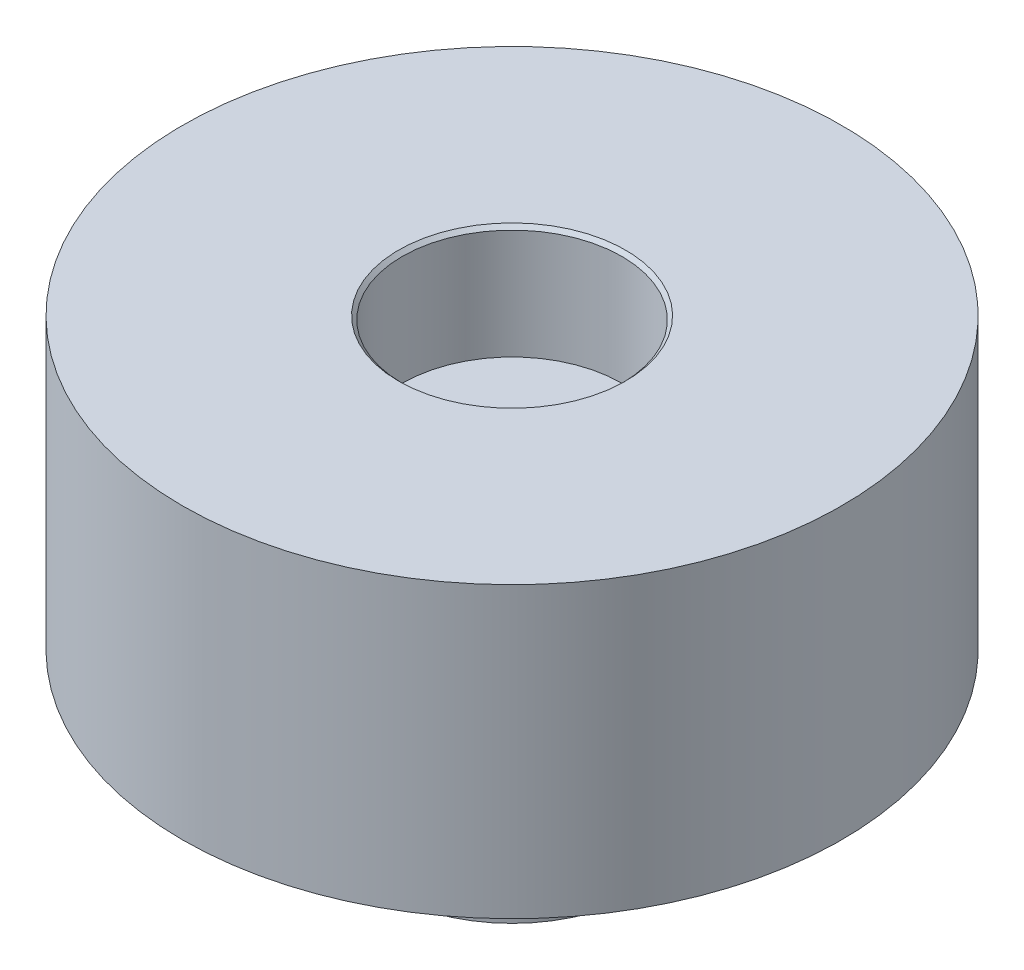
SolidWorks part; units mm, degrees
ref_plane "Front Plane" through (0, 0, 0) normal (0, 0, 1) x (1, 0, 0)
ref_plane "Top Plane" through (0, 0, 0) normal (0, 1, 0) x (1, 0, 0)
ref_plane "Right Plane" through (0, 0, 0) normal (1, 0, 0) x (0, 0, -1)
sketch "Sketch1" plane through (0, 0, 0) normal (0, 1, 0) x (1, 0, 0)
  circle A0 centre (0, 0) radius 9
  dimension "D1" = 18
extrude "Boss-Extrude1" add sketch "Sketch1" along normal blind 7.9
sketch "Sketch2" plane through (0, 7.9, 0) normal (0, 1, 0) x (1, 0, 0)
  circle A0 centre (0, 0) radius 3
  dimension "D1" = 6
extrude "Cut-Extrude1" cut sketch "Sketch2" against normal blind 3.1
sketch "Sketch3" plane through (0, 0, 0) normal (0, -1, 0) x (1, 0, 0)
  circle A0 centre (0, 0) radius 3.5
  dimension "D1" = 7
extrude "Boss-Extrude2" add sketch "Sketch3" along normal blind 4
hole_wizard "Tapped Hole for M2.5x0.45 Helicoil1" positions "Sketch4" profile "Sketch5" tap size "M2.5x0.45" standard "Helicoil® Metric"
sketch "Sketch4" plane through (0, -4, 0) normal (0, -1, 0) x (-1, 0, 0)
  point P0 (0, 0)
sketch "Sketch5" plane through (0, -4, 0) normal (1, 0, 0) x (0, 0, -1)
  line L0 (0, 0) -> (0, 7.6161)
  line L1 (0, 7.6161) -> (1.275, 6.85)
  line L2 (1.275, 6.85) -> (1.275, 0.3225)
  line L3 (1.275, 0.3225) -> (1.5975, 0)
  line L5 (1.5975, 0) -> (0, 0)
  line L6 (-1.275, 0.3225) -> (-1.5975, 0) construction
  line L10 (0, 7.6161) -> (-1.275, 6.85) construction
  line L11 (0, -6.35) -> (0, 107.95) construction
  dimension "Tap Drill Dia." = 2.55
  dimension "Tap Drill Depth" = 6.85
  dimension "Near C'Sink Dia." = 3.195
  dimension "Near C'Sink Angle" = 90
  dimension "Drill Angle" = 118
cosmetic thread "Hole Thread2" parameters "D1"=6.15, "D2"=3.145
chamfer "Chamfer1" distance 0.1 angle 45 1 edges at (0, 7.9, 3)
